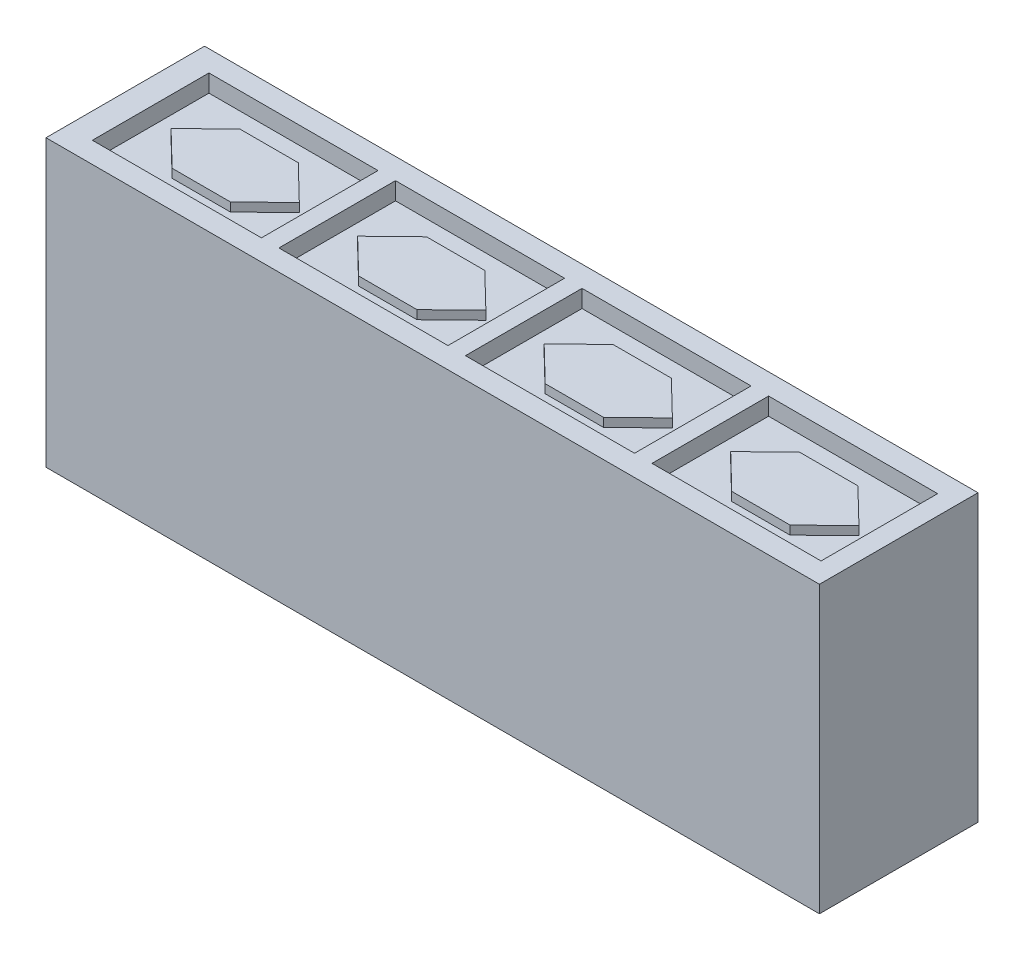
SolidWorks part; units mm, degrees
ref_plane "Front Plane" through (0, 0, 0) normal (0, 0, 1) x (1, 0, 0)
ref_plane "Top Plane" through (0, 0, 0) normal (0, 1, 0) x (1, 0, 0)
ref_plane "Right Plane" through (0, 0, 0) normal (1, 0, 0) x (0, 0, -1)
sketch "Sketch2" plane through (0, 0, 0) normal (0, 0, 1) x (1, 0, 0)
  line L1 (0, 0) -> (132.68, 0)
  line L2 (0, 0) -> (0, 48.96)
  line L3 (0, 48.96) -> (132.68, 48.96)
  line L4 (132.68, 0) -> (132.68, 48.96)
  dimension "D1" = 132.68
  dimension "D2" = 48.96
extrude "Boss-Extrude1" add sketch "Sketch2" along normal blind 27.2
sketch "Sketch3" plane through (0, 48.96, 0) normal (0, 1, 0) x (1, 0, 0)
  line L0 (0, -27.2) -> (0, 0) construction
  line L1 (4.355, -23.6) -> (33.355, -23.6)
  line L2 (4.355, -23.6) -> (4.355, -3.6)
  line L3 (4.355, -3.6) -> (33.355, -3.6)
  line L4 (33.355, -23.6) -> (33.355, -3.6)
  point P6 (0, -13.6)
  point P7 (4.355, -13.6)
  dimension "D1" = 29
  dimension "D2" = 20
  dimension "D3" = 4.355
extrude "Cut-Extrude1" cut sketch "Sketch3" against normal blind 3
sketch "Sketch4" plane through (0, 45.96, 0) normal (0, 1, 0) x (1, 0, 0)
  line L0 (0, -27.2) -> (0, 0) construction
  line L1 (13.855, -19.42) -> (23.855, -19.42)
  line L2 (13.855, -19.42) -> (13.855, -7.78)
  line L3 (13.855, -7.78) -> (23.855, -7.78)
  line L4 (23.855, -19.42) -> (23.855, -7.78)
  line L5 (33.355, -3.6) -> (4.355, -3.6) construction
  line L6 (23.855, -7.78) -> (29.855, -13.6)
  line L7 (29.855, -13.6) -> (23.855, -19.42)
  line L8 (23.855, -7.78) -> (23.855, -19.42)
  line L9 (13.855, -7.78) -> (7.855, -13.6)
  line L10 (7.855, -13.6) -> (13.855, -19.42)
  line L11 (13.855, -7.78) -> (13.855, -19.42)
  point P6 (0, -13.6)
  point P7 (13.855, -13.6)
  point P10 (18.855, -3.6)
  point P11 (18.855, -7.78)
  dimension "D1" = 10
  dimension "D2" = 11.64
  dimension "D3" = 6
  dimension "D4" = 6
extrude "Boss-Extrude2" add sketch "Sketch4" along normal blind 1.5 contours L9 L10 L2 | L1 L4 L3 L2 | L7 L6 L4
pattern_linear "LPattern1" count 4 spacing 32 along (1, 0, 0) of "Cut-Extrude1", "Boss-Extrude2"
